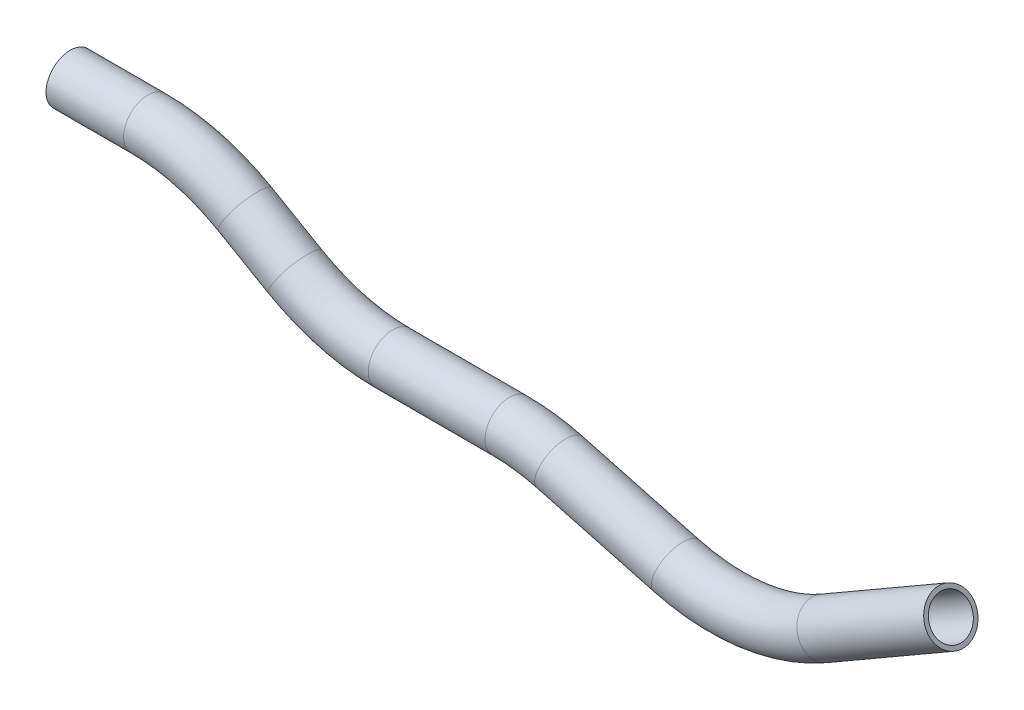
SolidWorks part; units mm, degrees
ref_plane "Front Plane" through (0, 0, 0) normal (0, 0, 1) x (1, 0, 0)
ref_plane "Top Plane" through (0, 0, 0) normal (0, 1, 0) x (1, 0, 0)
ref_plane "Right Plane" through (0, 0, 0) normal (1, 0, 0) x (0, 0, -1)
sketch "Sketch1" plane through (0, 0, 0) normal (0, 0, 1) x (1, 0, 0)
  line L0 (-53.3146, 60.8356) -> (-22.9324, 60.8356)
  line L1 (15.1676, 50.6268) -> (34.7957, 39.2945)
  line L2 (72.8957, 29.0856) -> (118.6461, 29.0856)
  line L3 (138.3681, 26.4892) -> (184.0612, 14.2457)
  line L4 (-53.3146, 60.8356) -> (24.5241, 60.8356) construction
  line L5 (34.7957, 39.2945) -> (15.1676, 50.6268) construction
  line L6 (15.1676, 50.6268) -> (-64.1659, 96.43) construction
  line L7 (15.1676, 50.6268) -> (34.7957, 39.2945) construction
  line L8 (34.7957, 39.2945) -> (103.8371, -0.5666) construction
  line L9 (118.6461, 29.0856) -> (72.8957, 29.0856) construction
  line L10 (72.8957, 29.0856) -> (1.4065, 29.0856) construction
  line L11 (72.8957, 29.0856) -> (118.6461, 29.0856) construction
  line L12 (241.8832, 21.8581) -> (291.5384, 50.5266)
  line L13 (72.8957, 29.0856) -> (118.6461, 29.0856) construction
  line L14 (118.6461, 29.0856) -> (263.2389, 29.0856) construction
  line L15 (184.0612, 14.2457) -> (138.3681, 26.4892) construction
  line L16 (138.3681, 26.4892) -> (-58.2583, 79.175) construction
  line L17 (138.3681, 26.4892) -> (184.0612, 14.2457) construction
  line L18 (184.0612, 14.2457) -> (512.0702, -73.644) construction
  line L19 (291.5384, 50.5266) -> (241.8832, 21.8581) construction
  line L20 (291.5384, 50.5266) -> (241.8832, 21.8581) construction
  line L21 (241.8832, 21.8581) -> (172.9352, -17.949) construction
  arc A0 (-22.9324, 60.8356) -> (15.1676, 50.6268) centre (-22.9324, -15.3644) cw
  arc A1 (34.7957, 39.2945) -> (72.8957, 29.0856) centre (72.8957, 105.2856) ccw
  arc A2 (118.6461, 29.0856) -> (138.3681, 26.4892) centre (118.6461, -47.1144) cw
  arc A3 (184.0612, 14.2457) -> (241.8832, 21.8581) centre (203.7832, 87.8493) ccw
  point P18 (52.478, 29.0856)
  point P19 (-2.5146, 60.8356)
  point P24 (214.5488, 6.0766)
  point P25 (128.678, 29.0856)
  dimension "D3" = 76.2
  dimension "D6" = 76.2
  dimension "D9" = 45
  dimension "D8" = 76.2
  dimension "D10" = 76.2
  dimension "D1" = 50.8
  dimension "D2" = 30
  dimension "D4" = 63.5
  dimension "D5" = 30
  dimension "D7" = 15
  dimension "D11" = 76.2
  dimension "D12" = 88.9
  dimension "D13" = 88.9
ref_plane "Plane1" through (-53.3146, 60.8356, 0) normal (1, 0, 0) x (0, 0, -1)
sketch "Sketch2" plane through (-53.3146, 60.8356, 0) normal (1, 0, 0) x (0, 0, -1)
  circle A0 centre (0, 0) radius 9.525
  circle A1 centre (0, 0) radius 7.874
  dimension "D1" = 15.748
  dimension "D2" = 19.05
sweep "Sweep1" add profiles "Sketch2" path "Sketch1"
